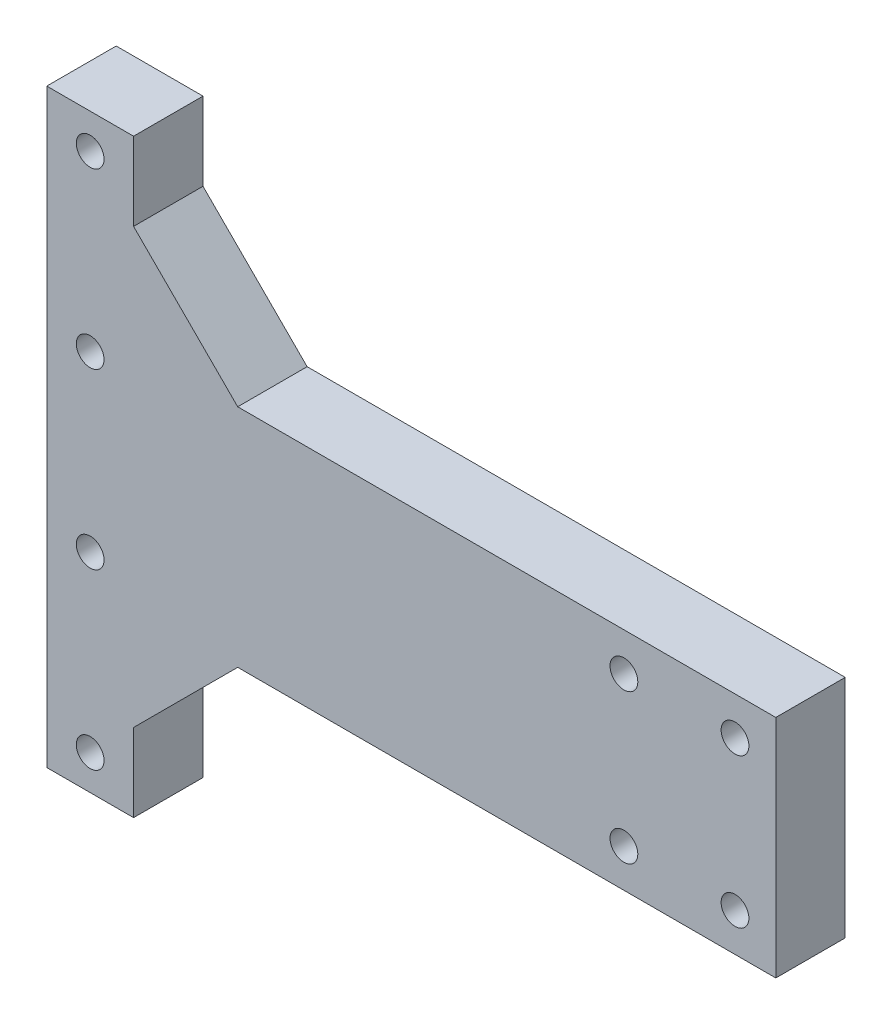
SolidWorks part; units mm, degrees
ref_plane "Front Plane" through (0, 0, 0) normal (0, 0, 1) x (1, 0, 0)
ref_plane "Top Plane" through (0, 0, 0) normal (0, 1, 0) x (1, 0, 0)
ref_plane "Right Plane" through (0, 0, 0) normal (1, 0, 0) x (0, 0, -1)
sketch "Sketch2" plane through (0, 0, 0) normal (0, 0, 1) x (1, 0, 0)
  line L0 (0, 0) -> (0, 340)
  line L1 (0, 340) -> (50, 340)
  line L2 (0, 0) -> (50, 0)
  line L4 (50, 340) -> (50, 295)
  line L5 (50, 0) -> (50, 45)
  line L6 (50, 295) -> (110, 235)
  line L7 (110, 235) -> (420, 235)
  line L8 (50, 45) -> (110, 105)
  line L9 (110, 105) -> (420, 105)
  line L10 (420, 235) -> (420, 105)
  dimension "D1" = 340
  dimension "D2" = 50
  dimension "D3" = 135
  dimension "D4" = 60
  dimension "D5" = 45
  dimension "D6" = 60
  dimension "D7" = 135
  dimension "D8" = 45
  dimension "D9" = 310
  dimension "D10" = 310
extrude "Boss-Extrude1" add sketch "Sketch2" along normal blind 40
sketch "Sketch3" plane through (0, 0, 40) normal (0, 0, 1) x (1, 0, 0)
  line L0 (25, 340) -> (25, 0) construction
  line L1 (50, 340) -> (0, 340) construction
  line L2 (0, 0) -> (50, 0) construction
  line L3 (25, 340) -> (25, 320) construction
  circle A0 centre (25, 320) radius 8
  circle A1 centre (25, 220) radius 8
  circle A2 centre (25, 120) radius 8
  circle A3 centre (25, 20) radius 8
  dimension "D2" = 16
  dimension "D1" = 20
  dimension "D3" = 4
extrude "Cut-Extrude1" cut sketch "Sketch3" against normal blind 172 and the other way blind 233
sketch "Sketch4" plane through (0, 0, 40) normal (0, 0, 1) x (1, 0, 0)
  line L0 (420, 105) -> (420, 235) construction
  line L1 (396.5, 127) -> (332.5, 127) construction
  line L2 (396.5, 127) -> (396.5, 213) construction
  line L3 (396.5, 213) -> (332.5, 213) construction
  line L4 (332.5, 127) -> (332.5, 213) construction
  line L5 (396.5, 170) -> (420, 170)
  circle A0 centre (396.5, 213) radius 8
  circle A1 centre (332.5, 213) radius 8
  circle A2 centre (332.5, 127) radius 8
  circle A3 centre (396.5, 127) radius 8
  dimension "D5" = 16
  dimension "D1" = 64
  dimension "D2" = 86
  dimension "D3" = 23.5
  dimension "D4" = 90
  dimension "D6" = 2
  dimension "D7" = 2
extrude "Cut-Extrude2" cut sketch "Sketch4" against normal blind 192 and the other way blind 81 contours A0 | A1 | A2 | A3
